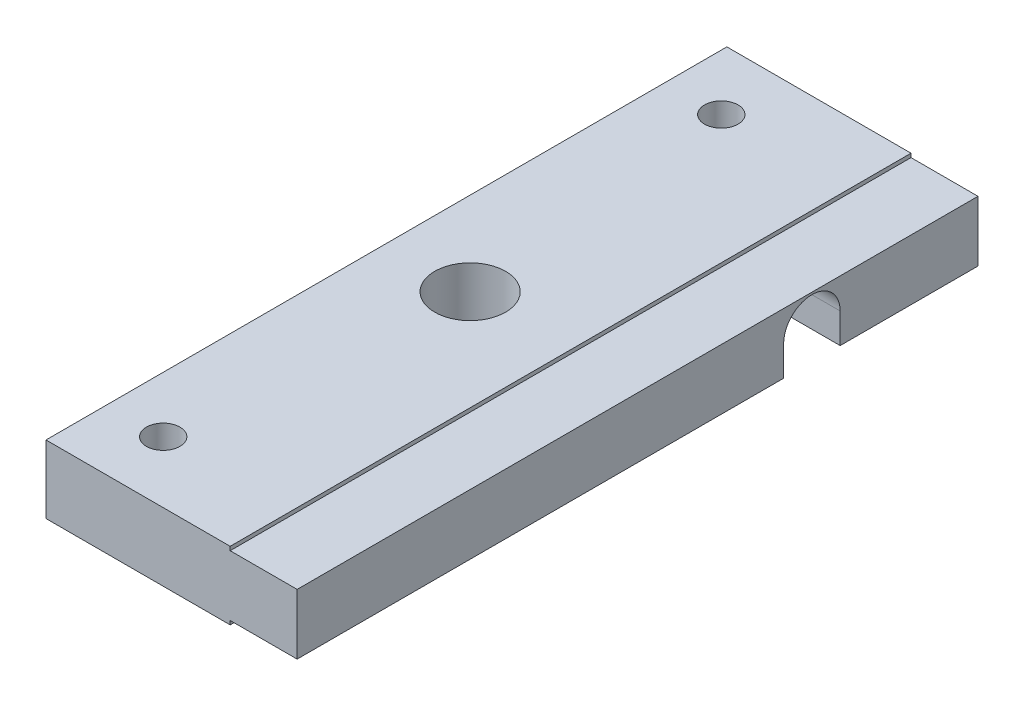
SolidWorks part; units mm, degrees
material "Generic Carbon Fiber"
ref_plane "Front Plane" through (0, 0, 0) normal (0, 0, 1) x (1, 0, 0)
ref_plane "Top Plane" through (0, 0, 0) normal (0, 1, 0) x (1, 0, 0)
ref_plane "Right Plane" through (0, 0, 0) normal (1, 0, 0) x (0, 0, -1)
sketch "Sketch1" plane through (0, 0, 0) normal (1, 0, 0) x (0, 0, -1)
  line L1 (0, -3.05) -> (61, -3.05)
  line L2 (0, -3.05) -> (0, 3.05)
  line L3 (0, 3.05) -> (61, 3.05)
  line L4 (61, -3.05) -> (61, 3.05)
  dimension "D1" = 61
  dimension "D2" = 6.1
extrude "Boss-Extrude1" add sketch "Sketch1" along normal blind 22.5
sketch "Sketch2" plane through (22.5, 0, 0) normal (1, 0, 0) x (0, 0, -1)
  line L0 (0, 3.05) -> (0, -3.05) construction
  line L1 (0, -2.7064) -> (61, -2.7064)
  line L2 (0, -2.7064) -> (0, 2.7064)
  line L3 (0, 2.7064) -> (61, 2.7064)
  line L4 (61, -2.7064) -> (61, 2.7064)
  line L5 (61, -3.05) -> (61, 3.05) construction
  line L7 (30.5, 3.05) -> (30.5, -3.05) construction
  line L8 (61, 3.05) -> (0, 3.05) construction
  line L9 (0, -3.05) -> (61, -3.05) construction
  line L10 (30.5, 0) -> (0, 0) construction
  dimension "D1" = 5.4128
extrude "Cut-Extrude1" cut sketch "Sketch2" against normal blind 6 flip side to cut
sketch "Sketch5" plane through (0, 0, 0) normal (-1, 0, 0) x (0, 0, 1)
  line L0 (-46.119, -0.019) -> (0, -0.019) construction
  line L2 (0, 3.05) -> (0, -3.05) construction
  line L3 (0, -3.05) -> (-61, -3.05) construction
  line L4 (-43.5866, -0.019) -> (-43.5866, -3.05)
  line L5 (-43.5866, -3.05) -> (-48.6514, -3.05)
  line L6 (-48.6514, -3.05) -> (-48.6514, -0.019)
  line L7 (-61, -3.05) -> (-61, 3.05) construction
  line L8 (-61, 2.7064) -> (0, 2.7064) construction
  arc A0 (-43.5866, -0.019) -> (-48.6514, -0.019) centre (-46.119, -0.019) ccw
  dimension "D1" = 5.0648
  dimension "D2" = 14.881
  dimension "D3" = 2.7254
extrude "Cut-Extrude3" cut sketch "Sketch5" against normal through all
sketch "Sketch6" plane through (0, 3.05, 0) normal (0, 1, 0) x (1, 0, 0)
  line L0 (0, 30.5) -> (22.5, 30.5) construction
  line L2 (22.5, 61) -> (22.5, 0) construction
  line L7 (0, 61) -> (0, 0) construction
  circle A0 centre (7.5, 30.5) radius 3.175
  dimension "D2" = 6.35
  dimension "D1" = 7.5
extrude "Cut-Extrude4" cut sketch "Sketch6" against normal through all
sketch "Sketch7" plane through (0, 3.05, 0) normal (0, 1, 0) x (1, 0, 0)
  line L0 (5, 61) -> (5, 0) construction
  line L1 (16.5, 61) -> (0, 61) construction
  line L2 (16.5, 0) -> (0, 0) construction
  line L3 (0, 61) -> (0, 0) construction
  line L4 (0, 30.5) -> (22.5, 30.5) construction
  line L5 (22.5, 61) -> (22.5, 0) construction
  circle A0 centre (5, 55.5) radius 1.5
  circle A1 centre (5, 5.5) radius 1.5
  dimension "D1" = 3
  dimension "D2" = 5
  dimension "D3" = 25
  dimension "D4" = 25
extrude "Cut-Extrude5" cut sketch "Sketch7" against normal through all
sketch "Sketch8" plane through (0, 0, 0) normal (0, 0, 1) x (1, 0, 0)
  line L0 (16.5, -2.7064) -> (16.5, -3.05) construction
  line L1 (14.5, -2.9814) -> (16.5, -2.9814)
  line L2 (14.5, -2.9814) -> (14.5, -3.05)
  line L3 (14.5, -3.05) -> (16.5, -3.05)
  line L4 (16.5, -2.9814) -> (16.5, -3.05)
  line L15 (16.5, 3.05) -> (14.5, 3.05)
  line L16 (16.5, 3.05) -> (16.5, 2.9814)
  line L17 (16.5, 2.9814) -> (14.5, 2.9814)
  line L18 (14.5, 3.05) -> (14.5, 2.9814)
  line L20 (16.5, 3.05) -> (0, 3.05) construction
  line L21 (14.5, -2.9814) -> (14.5, 2.9814) construction
  dimension "D2" = 0.0686
  dimension "D3" = 0.0686
  dimension "D5" = 2
sketch "Sketch9" plane through (0, 0, 0) normal (-1, 0, 0) x (0, 0, 1)
  line L0 (-46.119, 0.2006) -> (-49.9988, 0.2006) construction
  line L1 (-46.119, 0.2006) -> (-46.119, -2.1806) construction
  line L2 (-49.9988, 0.2006) -> (-61, 0.2006) construction
  line L3 (-61, -3.05) -> (-61, 3.05) construction
  line L4 (-46.119, 2.5819) -> (-46.119, 3.05) construction
  line L5 (-61, 3.05) -> (0, 3.05) construction
  line L6 (-49.9988, 0.2006) -> (-49.9988, -3.05)
  line L7 (0, -3.05) -> (-43.5866, -3.05) construction
  line L8 (-49.9988, -3.05) -> (-42.2391, -3.05)
  line L9 (-42.2391, -3.05) -> (-42.2392, 0.2006)
  ellipse E0 centre (-46.119, 0.2006) end of major axis (-42.2392, 0.2006) minor radius 2.3812 (-42.2392, 0.2006) -> (-49.9988, 0.2006) ccw
  dimension "D1" = 0.4681
  dimension "D2" = 2.3813
  dimension "D3" = 3.8798
  dimension "D4" = 14.881
extrude "Cut-Extrude6" [suppressed] cut sketch "Sketch9" against normal through all
